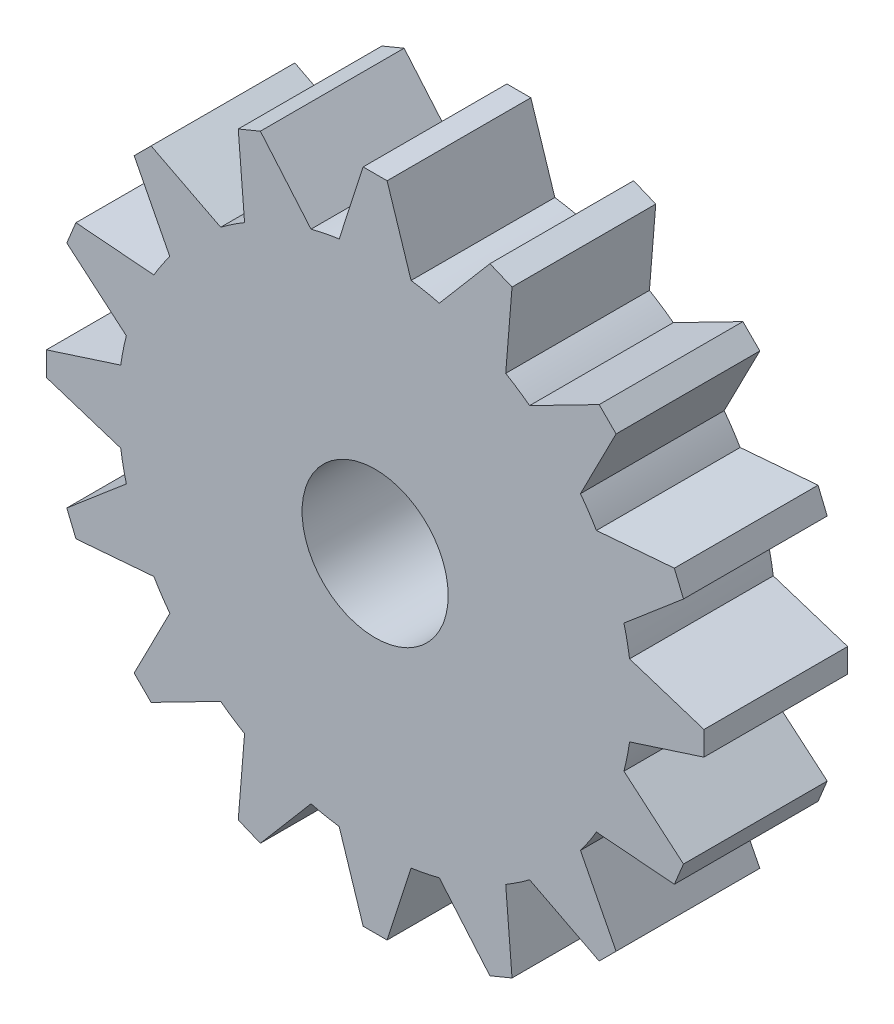
SolidWorks part; units mm, degrees
ref_plane "Front Plane" through (0, 0, 0) normal (0, 0, 1) x (1, 0, 0)
ref_plane "Top Plane" through (0, 0, 0) normal (0, 1, 0) x (1, 0, 0)
ref_plane "Right Plane" through (0, 0, 0) normal (1, 0, 0) x (0, 0, -1)
sketch "Sketch1" plane through (0, 0, 0) normal (0, 0, 1) x (1, 0, 0)
  circle A0 centre (0, 0) radius 3.05
  circle A1 centre (0, 0) radius 10.7261
  point P6 (0, 0)
  dimension "D1" = 6.1
  dimension "D3" = 21.4522
extrude "Boss-Extrude1" add sketch "Sketch1" along normal blind 6 contours A1 A0
sketch "Sketch3" plane through (0, 0, 6) normal (0, 0, 1) x (1, 0, 0)
  line L0 (-10.7261, 0) -> (0, 0) construction
  line L1 (0, 0) -> (-10.7261, 0) construction
  line L2 (-10.7261, 0) -> (-13.7261, 0) construction
  line L3 (-13.7261, 0) -> (-13.7261, 0.5)
  line L4 (0, 0) -> (-9.9096, 4.1047) construction
  line L5 (-13.7261, 0.5) -> (-10.6206, 1.5008)
  line L6 (-10.7261, 0) -> (-9.9096, 4.1047) construction
  line L7 (-10.3179, 2.0524) -> (-22.2066, 4.4172) construction
  line L8 (-9.9096, 4.1047) -> (-12.6813, 5.2528) construction
  line L9 (-12.8726, 4.7908) -> (-10.3865, 2.6778)
  line L10 (-12.6813, 5.2528) -> (-12.8726, 4.7908)
  line L11 (-10.0594, 9.3523) -> (-8.5711, 6.4487)
  line L12 (-9.7058, 9.7058) -> (-10.0594, 9.3523)
  line L13 (-12.4899, 5.7147) -> (-9.2378, 5.4509)
  line L14 (-12.6813, 5.2528) -> (-12.4899, 5.7147)
  line L15 (-5.7147, 12.4899) -> (-5.4509, 9.2378)
  line L16 (-5.2528, 12.6813) -> (-5.7147, 12.4899)
  line L17 (-9.3523, 10.0594) -> (-6.4487, 8.5711)
  line L18 (-9.7058, 9.7058) -> (-9.3523, 10.0594)
  line L19 (-0.5, 13.7261) -> (-1.5008, 10.6206)
  line L20 (0, 13.7261) -> (-0.5, 13.7261)
  line L21 (-4.7908, 12.8726) -> (-2.6778, 10.3865)
  line L22 (-5.2528, 12.6813) -> (-4.7908, 12.8726)
  line L23 (4.7908, 12.8726) -> (2.6778, 10.3865)
  line L24 (5.2528, 12.6813) -> (4.7908, 12.8726)
  line L25 (0.5, 13.7261) -> (1.5008, 10.6206)
  line L26 (0, 13.7261) -> (0.5, 13.7261)
  line L27 (9.3523, 10.0594) -> (6.4487, 8.5711)
  line L28 (9.7058, 9.7058) -> (9.3523, 10.0594)
  line L29 (5.7147, 12.4899) -> (5.4509, 9.2378)
  line L30 (5.2528, 12.6813) -> (5.7147, 12.4899)
  line L31 (12.4899, 5.7147) -> (9.2378, 5.4509)
  line L32 (12.6813, 5.2528) -> (12.4899, 5.7147)
  line L33 (10.0594, 9.3523) -> (8.5711, 6.4487)
  line L34 (9.7058, 9.7058) -> (10.0594, 9.3523)
  line L35 (13.7261, 0.5) -> (10.6206, 1.5008)
  line L36 (13.7261, 0) -> (13.7261, 0.5)
  line L37 (12.8726, 4.7908) -> (10.3865, 2.6778)
  line L38 (12.6813, 5.2528) -> (12.8726, 4.7908)
  line L39 (12.8726, -4.7908) -> (10.3865, -2.6778)
  line L40 (12.6813, -5.2528) -> (12.8726, -4.7908)
  line L41 (13.7261, -0.5) -> (10.6206, -1.5008)
  line L42 (13.7261, 0) -> (13.7261, -0.5)
  line L43 (10.0594, -9.3523) -> (8.5711, -6.4487)
  line L44 (9.7058, -9.7058) -> (10.0594, -9.3523)
  line L45 (12.4899, -5.7147) -> (9.2378, -5.4509)
  line L46 (12.6813, -5.2528) -> (12.4899, -5.7147)
  line L47 (5.7147, -12.4899) -> (5.4509, -9.2378)
  line L48 (5.2528, -12.6813) -> (5.7147, -12.4899)
  line L49 (9.3523, -10.0594) -> (6.4487, -8.5711)
  line L50 (9.7058, -9.7058) -> (9.3523, -10.0594)
  line L51 (0.5, -13.7261) -> (1.5008, -10.6206)
  line L52 (0, -13.7261) -> (0.5, -13.7261)
  line L53 (4.7908, -12.8726) -> (2.6778, -10.3865)
  line L54 (5.2528, -12.6813) -> (4.7908, -12.8726)
  line L55 (-4.7908, -12.8726) -> (-2.6778, -10.3865)
  line L56 (-5.2528, -12.6813) -> (-4.7908, -12.8726)
  line L57 (-0.5, -13.7261) -> (-1.5008, -10.6206)
  line L58 (0, -13.7261) -> (-0.5, -13.7261)
  line L59 (-9.3523, -10.0594) -> (-6.4487, -8.5711)
  line L60 (-9.7058, -9.7058) -> (-9.3523, -10.0594)
  line L61 (-5.7147, -12.4899) -> (-5.4509, -9.2378)
  line L62 (-5.2528, -12.6813) -> (-5.7147, -12.4899)
  line L63 (-12.4899, -5.7147) -> (-9.2378, -5.4509)
  line L64 (-12.6813, -5.2528) -> (-12.4899, -5.7147)
  line L65 (-10.0594, -9.3523) -> (-8.5711, -6.4487)
  line L66 (-9.7058, -9.7058) -> (-10.0594, -9.3523)
  line L67 (-13.7261, -0.5) -> (-10.6206, -1.5008)
  line L68 (-13.7261, 0) -> (-13.7261, -0.5)
  line L69 (-12.8726, -4.7908) -> (-10.3865, -2.6778)
  line L70 (-12.6813, -5.2528) -> (-12.8726, -4.7908)
  circle A0 centre (0, 0) radius 10.7261 construction
  circle A1 centre (0, 0) radius 10.7261
  circle A4 centre (0, 0) radius 10.7261 construction
  point P6 (-13.7261, 0)
  point P20 (0, 0)
  point P102 (0, 0)
  point P109 (0, 0)
  dimension "D2" = 1.2
  dimension "D3" = 22.5
  dimension "D4" = 0.5
  dimension "D1" = 3
  dimension "D5" = 16
extrude "Boss-Extrude2" add sketch "Sketch3" against normal up to surface (6 mm away) up to face at (3.05, 0, 0)
equation "\"teethnum\"=17"
equation "\"D3@Sketch3\"=360/16"
